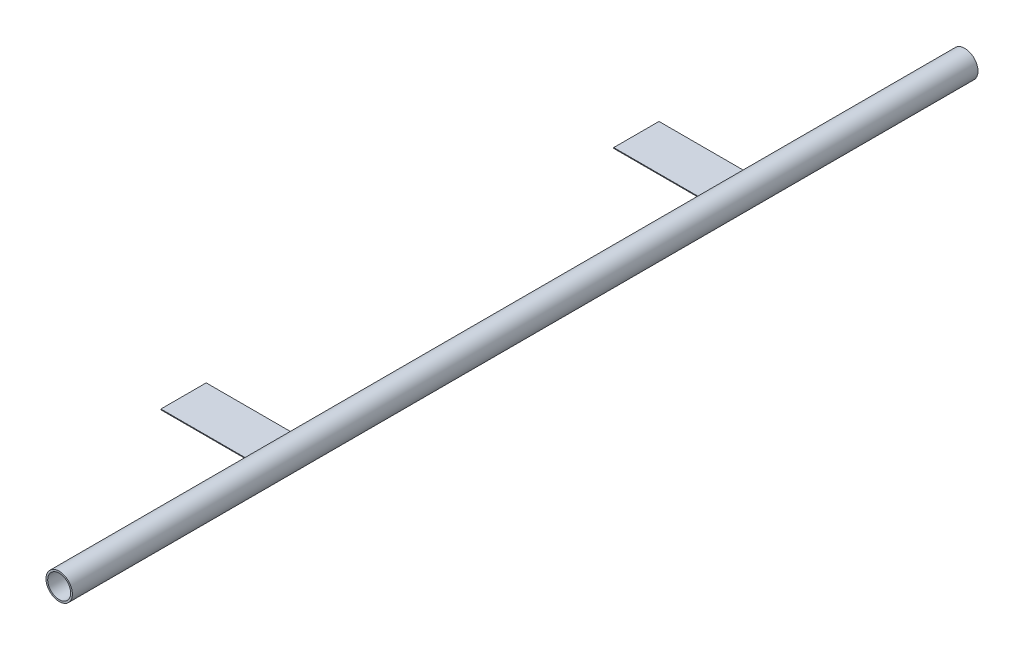
SolidWorks part; units mm, degrees
material "PVC Rigid"
ref_plane "Front Plane" through (0, 0, 0) normal (0, 0, 1) x (1, 0, 0)
ref_plane "Top Plane" through (0, 0, 0) normal (0, 1, 0) x (1, 0, 0)
ref_plane "Right Plane" through (0, 0, 0) normal (1, 0, 0) x (0, 0, -1)
sketch "Sketch1" plane through (0, 0, 0) normal (0, 0, 1) x (1, 0, 0)
  circle A0 centre (0, 0) radius 44.45
  circle A2 centre (0, 0) radius 38.6334
  dimension "D1" = 88.9
  dimension "D2" = 77.2668
extrude "Boss-Extrude1" add sketch "Sketch1" along normal blind 3048
sketch "Sketch2" plane through (0, 0, 0) normal (1, 0, 0) x (0, 0, -1)
  circle A0 centre (-1828.8, 0) radius 12.7
  dimension "D1" = 25.4
  dimension "D2" = 1219.2
extrude "Cut-Extrude1" cut sketch "Sketch2" against normal through all
sketch "Sketch3" plane through (0, 0, 0) normal (0, 1, 0) x (1, 0, 0)
  line L0 (-38.6334, 0) -> (-38.6334, -1816.1) construction
  line L1 (-38.6334, -685.8) -> (-343.4334, -685.8)
  line L2 (-38.6334, -685.8) -> (-38.6334, -838.2)
  line L3 (-38.6334, -838.2) -> (-343.4334, -838.2)
  line L4 (-343.4334, -685.8) -> (-343.4334, -838.2)
  line L5 (0, -3048) -> (0, 0) construction
  line L6 (179.4492, -1524) -> (-179.4492, -1524) construction
  line L7 (-38.6334, -2209.8) -> (-343.4334, -2209.8)
  line L8 (-343.4334, -2362.2) -> (-343.4334, -2209.8)
  line L9 (-38.6334, -2362.2) -> (-343.4334, -2362.2)
  line L10 (-38.6334, -2362.2) -> (-38.6334, -2209.8)
  line L11 (-44.45, -3048) -> (44.45, -3048) construction
  line L12 (44.45, 0) -> (-44.45, 0) construction
  line L13 (179.4492, -1524) -> (179.4492, 0) construction
  line L14 (-38.6334, -762) -> (-343.4334, -762) construction
  point P18 (0, -1524)
  dimension "D1" = 304.8
  dimension "D2" = 152.4
  dimension "D3" = 762
extrude "Boss-Extrude2" add sketch "Sketch3" along normal blind 2.54
sketch "Sketch4" plane through (0, 2.54, 0) normal (0, 1, 0) x (1, 0, 0)
  line L0 (-1237.2404, -1967.6186) -> (-1710.4897, -1967.6186) construction
  line L1 (-294.9965, -2563.4664) -> (-294.9965, -2754.133) construction
